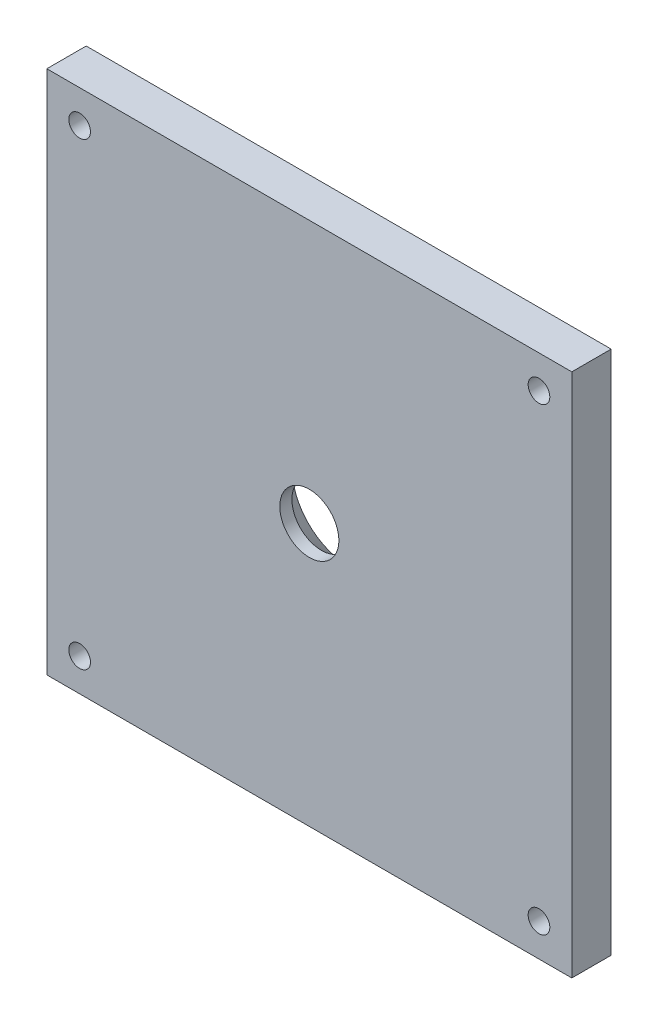
SolidWorks part; units mm, degrees
ref_plane "Ebene vorne" through (0, 0, 0) normal (0, 0, 1) x (1, 0, 0)
ref_plane "Ebene oben" through (0, 0, 0) normal (0, 1, 0) x (1, 0, 0)
ref_plane "Ebene rechts" through (0, 0, 0) normal (1, 0, 0) x (0, 0, -1)
sketch "Skizze1" plane through (0, 0, 0) normal (0, 0, 1) x (1, 0, 0)
  line L0 (0, 35.6386) -> (0, -31.0153) construction
  line L1 (47.3898, 0) -> (-50.8573, 0) construction
  line L3 (-40, 40) -> (40, 40)
  line L4 (-40, 40) -> (-40, -40)
  line L5 (-40, -40) -> (40, -40)
  line L6 (40, 40) -> (40, -40)
  circle A0 centre (0, 0) radius 2.5
  dimension "D2" = 5
  dimension "D1" = 80
extrude "Aufsatz-Linear austragen1" add sketch "Skizze1" along normal blind 6
chamfer "Fase1" [suppressed] distance 4 angle 45
sketch "Skizze5" plane through (0, 0, 0) normal (0, 0, -1) x (-1, 0, 0)
  line L0 (35, -40) -> (35, 40) construction
  line L1 (-40, 40) -> (40, 40) construction
  line L3 (40, 35) -> (-40, 35) construction
  line L4 (40, 40) -> (40, -40) construction
  line L5 (-40, -40) -> (-40, 40) construction
  line L6 (-40, -35) -> (40, -35) construction
  line L7 (-35, 40) -> (-35, -40) construction
  point P19 (0, 0)
  dimension "D1" = 5
  dimension "D2" = 4
hole_wizard "M4 Gewindebohrung2" positions "Skizze7" profile "Skizze6" tap size "M4" standard "DIN"
sketch "Skizze7" plane through (0, 0, 0) normal (0, 0, -1) x (-1, 0, 0)
  line L0 (35, -40) -> (35, 40) construction
  line L1 (40, 35) -> (-40, 35) construction
  line L2 (-40, -35) -> (40, -35) construction
  line L3 (-35, 40) -> (-35, -40) construction
  point P0 (35, 35)
  point P6 (35, -35)
  point P10 (-35, -35)
  point P14 (-35, 35)
sketch "Skizze6" plane through (-35, 35, 0) normal (1, 0, 0) x (0, 1, 0)
  line L0 (0, 0) -> (0, 12.4914)
  line L1 (0, 12.4914) -> (1.65, 11.5)
  line L2 (1.65, 11.5) -> (1.65, 0)
  line L5 (1.65, 0) -> (0, 0)
  line L10 (0, 12.4914) -> (-1.65, 11.5) construction
  line L11 (0, -6.35) -> (0, 107.95) construction
  dimension "Bohrerdurchmesser" = 3.3
  dimension "Bohrungstiefe" = 11.5
  dimension "Spitzenwinkel" = 118
cosmetic thread "Bohrungsgewinde2"
cosmetic thread "Bohrungsgewinde3"
cosmetic thread "Bohrungsgewinde4"
cosmetic thread "Bohrungsgewinde5"
hole_wizard "Formsenkung für M8 Linsensenkschraube1" positions "Skizze9" profile "Skizze8" countersink size "M8" standard "ANSI Metrisch" end condition through all
sketch "Skizze9" plane through (0, 0, 0) normal (0, 0, -1) x (-1, 0, 0)
  point P0 (0, 0)
sketch "Skizze8" plane through (0, 0, 0) normal (1, 0, 0) x (0, 1, 0)
  line L0 (0, 0) -> (0, 6)
  line L1 (0, 6) -> (4.5, 6)
  line L2 (4.5, 6) -> (4.5, 4.15)
  line L3 (4.5, 4.15) -> (8.65, 0)
  line L5 (8.65, 0) -> (0, 0)
  line L6 (-4.5, 4.15) -> (-8.65, 0) construction
  line L11 (0, -6.35) -> (0, 107.95) construction
  dimension "Bohrerdurchmesser" = 9
  dimension "Bohrungstiefe" = 6
  dimension "Senkdurchmesser (Oben)" = 17.3
  dimension "Senkwinkel (Oben)" = 90
